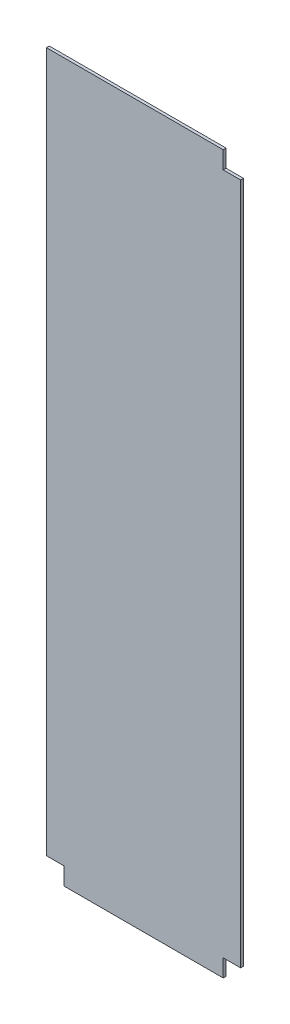
SolidWorks part; units mm, degrees
ref_plane "Front Plane" through (0, 0, 0) normal (0, 0, 1) x (1, 0, 0)
ref_plane "Top Plane" through (0, 0, 0) normal (0, 1, 0) x (1, 0, 0)
ref_plane "Right Plane" through (0, 0, 0) normal (1, 0, 0) x (0, 0, -1)
sketch "Sketch1" plane through (0, 0, 0) normal (0, 0, 1) x (1, 0, 0)
  line L1 (0, 0) -> (215.9, 0)
  line L2 (0, 0) -> (0, 797.2552)
  line L3 (0, 797.2552) -> (215.9, 797.2552)
  line L4 (215.9, 0) -> (215.9, 797.2552)
  dimension "D1" = 797.2552
  dimension "D2" = 215.9
extrude "Boss-Extrude1" add sketch "Sketch1" along normal blind 3.175
sketch "Sketch2" plane through (0, 0, 3.175) normal (0, 0, 1) x (1, 0, 0)
  line L1 (215.9, 797.2552) -> (196.469, 797.2552)
  line L2 (215.9, 797.2552) -> (215.9, 777.8242)
  line L3 (215.9, 777.8242) -> (196.469, 777.8242)
  line L4 (196.469, 797.2552) -> (196.469, 777.8242)
  line L5 (215.9, 0) -> (196.469, 0)
  line L6 (215.9, 0) -> (215.9, 19.431)
  line L7 (215.9, 19.431) -> (196.469, 19.431)
  line L8 (196.469, 0) -> (196.469, 19.431)
  line L9 (0, 0) -> (19.431, 0)
  line L10 (0, 0) -> (0, 19.431)
  line L11 (0, 19.431) -> (19.431, 19.431)
  line L12 (19.431, 0) -> (19.431, 19.431)
  dimension "D1" = 19.431
extrude "Cut-Extrude1" cut sketch "Sketch2" against normal through all
hole_wizard "#8 Clearance Hole1" positions "Sketch4" profile "Sketch5" hole size "#8" standard "ANSI Inch"
sketch "Sketch4" plane through (0, 0, 3.175) normal (0, 0, 1) x (1, 0, 0)
  line L1 (215.9, 19.431) -> (215.9, 777.8242) construction
  line L2 (196.469, 797.2552) -> (0, 797.2552) construction
  point P0 (135.511, 761.364)
  point P2 (115.1255, 663.9052)
  point P4 (162.3695, 663.9052)
  dimension "D1" = 99.568
  dimension "D2" = 101.092
  dimension "D3" = 47.244
  dimension "D4" = 53.5305
  dimension "D5" = 133.35
sketch "Sketch5" plane through (135.511, 761.364, 3.175) normal (1, 0, 0) x (0, -1, 0)
  line L0 (0, 0) -> (0, 3.175)
  line L1 (0, 3.175) -> (2.2479, 3.175)
  line L2 (2.2479, 3.175) -> (2.2479, 0)
  line L5 (2.2479, 0) -> (0, 0)
  line L11 (0, -6.35) -> (0, 107.95) construction
  dimension "Thru Hole Dia." = 4.4958
  dimension "Thru Hole Depth" = 3.175
